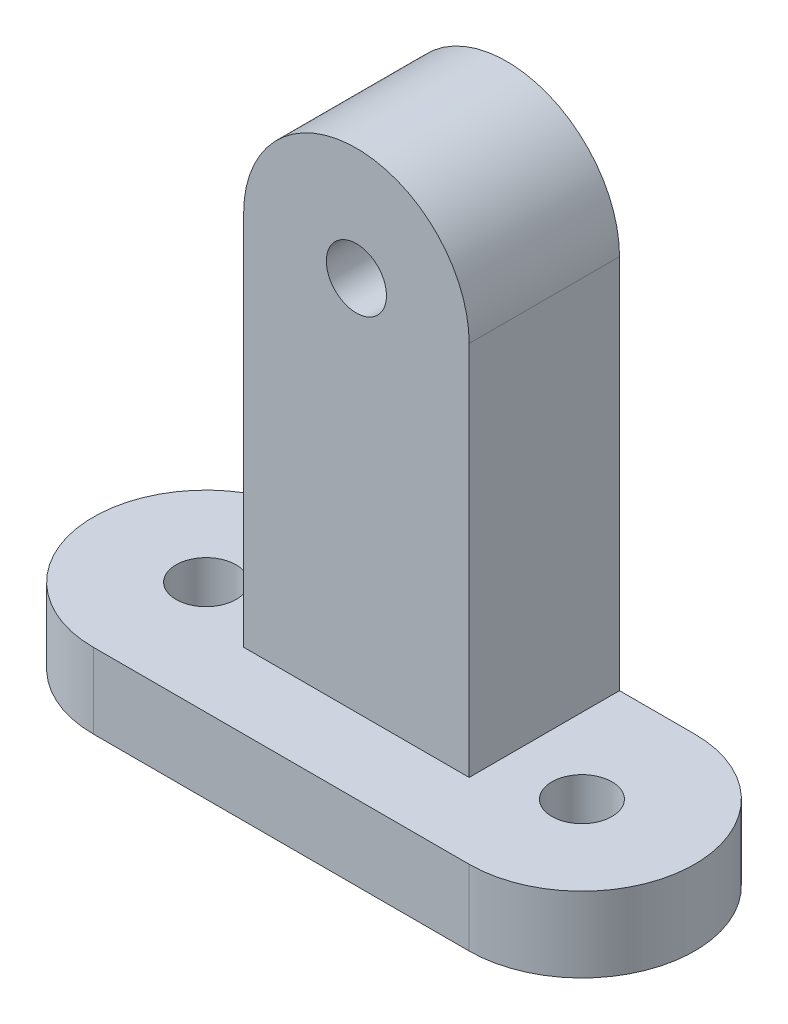
SolidWorks part; units mm, degrees
ref_plane "Front Plane" through (0, 0, 0) normal (0, 0, 1) x (1, 0, 0)
ref_plane "Top Plane" through (0, 0, 0) normal (0, 1, 0) x (1, 0, 0)
ref_plane "Right Plane" through (0, 0, 0) normal (1, 0, 0) x (0, 0, -1)
sketch "Sketch1" plane through (0, 0, 0) normal (0, 1, 0) x (1, 0, 0)
  line L1 (0, 0) -> (25, 0)
  line L2 (0, 0) -> (0, 15) construction
  line L3 (0, 15) -> (25, 15)
  line L4 (25, 0) -> (25, 15) construction
  arc A0 (0, 15) -> (0, 0) centre (0, 7.5) ccw
  arc A1 (25, 15) -> (25, 0) centre (25, 7.5) cw
  circle A2 centre (0, 7.5) radius 2
  circle A4 centre (25, 7.5) radius 2
  dimension "D3" = 4
  dimension "D4" = 4
  dimension "D1" = 15
  dimension "D2" = 25
extrude "Boss-Extrude1" add sketch "Sketch1" along normal blind 5
sketch "Sketch3" plane through (0, 0, -15) normal (0, 0, -1) x (-1, 0, 0)
  line L0 (-25, 5) -> (0, 5) construction
  line L1 (-20, 5) -> (-5, 5)
  line L2 (-20, 5) -> (-20, 30)
  line L3 (-20, 30) -> (-5, 30) construction
  line L4 (-5, 5) -> (-5, 30)
  line L5 (-12.5, 30) -> (-12.5, 5) construction
  arc A0 (-20, 30) -> (-5, 30) centre (-12.5, 30) cw
  circle A1 centre (-12.5, 30) radius 2
  dimension "D1" = 4
  dimension "D2" = 15
  dimension "D3" = 25
extrude "Boss-Extrude2" add sketch "Sketch3" against normal blind 10
